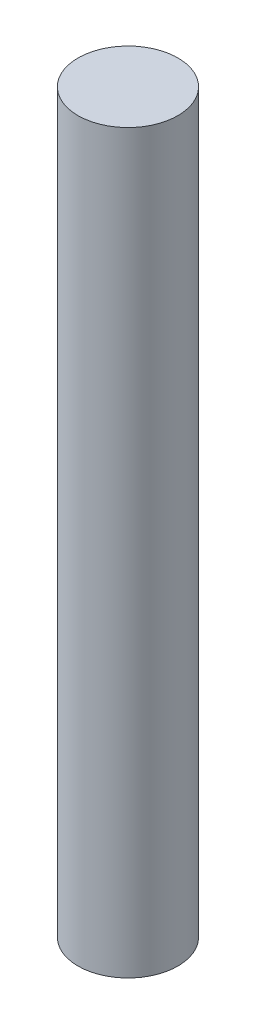
SolidWorks part; units mm, degrees
ref_plane "Front Plane" through (0, 0, 0) normal (0, 0, 1) x (1, 0, 0)
ref_plane "Top Plane" through (0, 0, 0) normal (0, 1, 0) x (1, 0, 0)
ref_plane "Right Plane" through (0, 0, 0) normal (1, 0, 0) x (0, 0, -1)
sketch "Sketch1" plane through (0, 0, 0) normal (0, 1, 0) x (1, 0, 0)
  circle A0 centre (0, 0) radius 27.2
  dimension "D1" = 54.4
extrude "Boss-Extrude1" add sketch "Sketch1" along normal blind 401
equation "\"Motor_Length\" = 401mm"
equation "\"Motor_OD\" = 54.4mm"
equation "\"D1@Sketch1\"=\"Motor_OD\""
equation "\"D1@Boss-Extrude1\"=\"Motor_Length\""
equation "\"Aft_Section_Length\" = 32in"
equation "\"Mid_Coupler_Length\" = 12in"
equation "\"AB_Coupler_OD_Length\"= 1in"
equation "\"AB_Coupling_Section_Length\"= 0.375in"
equation "\"AB_Coupler_Length\"= \"AB_Coupler_OD_Length\" + \"AB_Coupling_Section_Length\" * 2"
equation "\"Cutout_Angle\" = 60"
equation "\"AB_Paddle_Height\" = 0.375in"
equation "\"AB_Coupler_Num_Screws\"= 4"
equation "\"Num_Cutouts\" = 4"
equation "\"AB_Coupler_OD\"= 4.024in"
equation "\"AB_Coupler_ID\"= 3.7in"
equation "\"AB_Coupler_Surface_Diameter\"= 3.899in"
equation "\"AB_Coupling_Screw_Diameter\"= 4.5mm"
equation "\"AB_Central_Bushing_Length\" = 0.75in"
equation "\"Lead_Screw_Dist\" = 2in"
equation "\"Lead_Screw_Diam\" = 0.375in"
equation "\"Lead_Screw_Length\" = \"Mid_Coupler_Length\" + 2*0.375in + 2*0.5in"
equation "\"Paddle_Pin_Offset\" = 0.25in"
equation "\"Paddle_Pin_Radius\" = 2.25*2/3in"
equation "\"Paddle_Gear_OD\" = 3.2in"
equation "\"Fwd_BKHD_From_Top\" = 18in"
equation "\"Body_Tube_OD\"= 4.024in"
equation "\"Body_Tube_ID\"= 3.90in"
equation "\"Coupler_OD\" = 3.899in"
equation "\"Coupler_ID\" = 3.755in"
equation "\"Fwd_Section_Length\" = 20in"
equation "\"Mid_Section_Length\" = 4in"
equation "\"Aft_Upper_Tube_Length\" = 10in"
equation "\"Aft_Lower_Tube_Length\" = 18in"
equation "\"Nosecone_Coupler_Length\" = 5in"
equation "\"Avionics_Bulkhead_Thickness\" = 0.25in"
equation "\"Avionics_Bulkhead_Lip\" = 0.125in"
equation "\"Avionics_Board_Length\" = \"Mid_Coupler_Length\" - 2*\"Avionics_Bulkhead_Lip\""
equation "\"Lead_Screw_Hole_Diam\" = 0.386in"
equation "\"Centering_Ring_Cutout_Dia\"= 1in"
